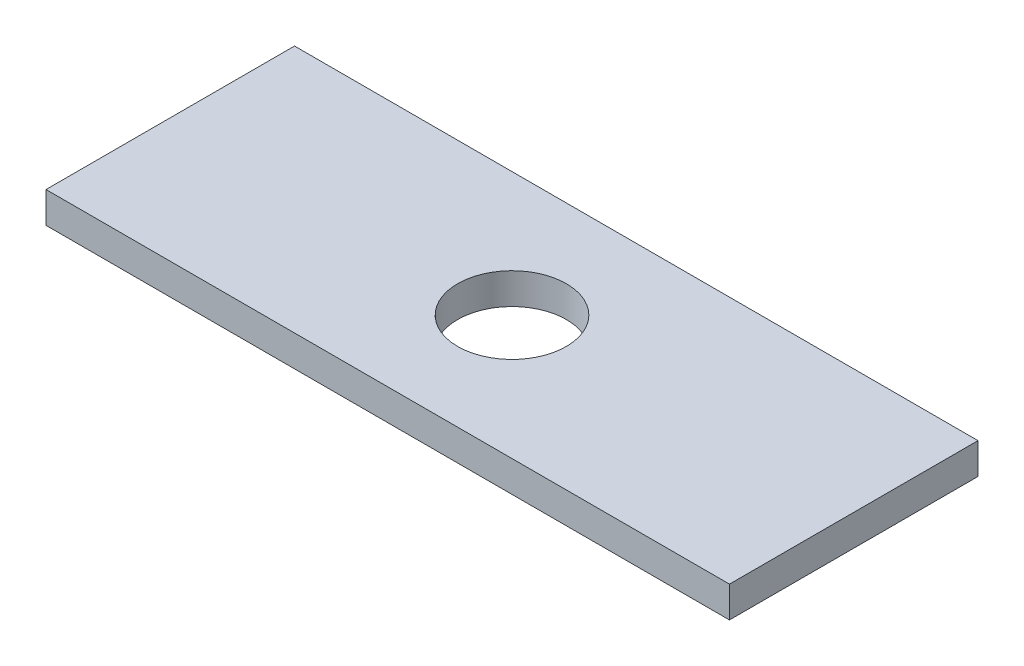
SolidWorks part; units mm, degrees
ref_plane "Front Plane" through (0, 0, 0) normal (0, 0, 1) x (1, 0, 0)
ref_plane "Top Plane" through (0, 0, 0) normal (0, 1, 0) x (1, 0, 0)
ref_plane "Right Plane" through (0, 0, 0) normal (1, 0, 0) x (0, 0, -1)
sketch "Sketch1" plane through (0, 0, 0) normal (0, 1, 0) x (1, 0, 0)
  line L1 (0, 0) -> (139.7, 0)
  line L2 (0, 0) -> (0, -50.8)
  line L3 (0, -50.8) -> (139.7, -50.8)
  line L4 (139.7, 0) -> (139.7, -50.8)
  dimension "D1" = 139.7
  dimension "D2" = 50.8
extrude "Boss-Extrude1" add sketch "Sketch1" along normal blind 6.35
sketch "Sketch2" plane through (0, 6.35, 0) normal (0, 1, 0) x (1, 0, 0)
  line L0 (69.85, 0) -> (69.85, -50.8) construction
  line L1 (139.7, 0) -> (0, 0) construction
  line L2 (0, -50.8) -> (139.7, -50.8) construction
  line L3 (0, -25.4) -> (69.85, -25.4) construction
  line L4 (-7.4478, -25.4) -> (0, -25.4) construction
  line L5 (0, 0) -> (0, -50.8) construction
  line L6 (69.85, -25.4) -> (139.7, -25.4) construction
  line L7 (139.7, -50.8) -> (139.7, 0) construction
  circle A0 centre (69.85, -25.4) radius 11.1125
extrude "Cut-Extrude1" cut sketch "Sketch2" against normal through all
